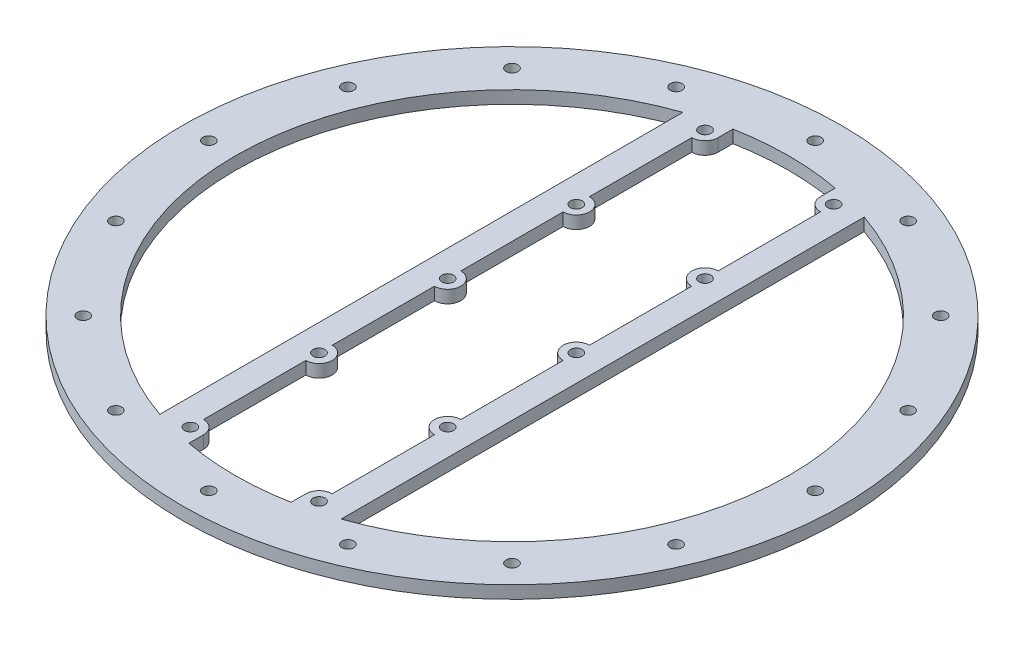
SolidWorks part; units mm, degrees
ref_plane "Front" through (0, 0, 0) normal (0, 0, 1) x (1, 0, 0)
ref_plane "Top" through (0, 0, 0) normal (0, 1, 0) x (1, 0, 0)
ref_plane "Right" through (0, 0, 0) normal (1, 0, 0) x (0, 0, -1)
sketch "Sketch1" plane through (0, 0, 0) normal (0, 1, 0) x (1, 0, 0)
  line L0 (0, 73.025) -> (0, -73.025) construction
  line L1 (73.025, 0) -> (-73.025, 0) construction
  line L3 (15.494, 64.8498) -> (15.494, -64.8498) construction
  line L4 (-15.494, 64.8498) -> (-15.494, -64.8498) construction
  line L5 (64.8498, -15.494) -> (-64.8498, -15.494) construction
  line L7 (73.025, -15.494) -> (-73.025, -15.494) construction
  line L8 (64.8498, 15.494) -> (-64.8498, 15.494) construction
  circle A0 centre (0, 0) radius 79.375
  circle A1 centre (0, 0) radius 66.675
  circle A2 centre (0, 0) radius 73.025 construction
  circle A3 centre (0, 73.025) radius 1.4224
  circle A4 centre (27.9455, 67.4663) radius 1.4224
  circle A5 centre (51.6365, 51.6365) radius 1.4224
  circle A6 centre (67.4663, 27.9455) radius 1.4224
  circle A7 centre (73.025, 0) radius 1.4224
  circle A8 centre (67.4663, -27.9455) radius 1.4224
  circle A9 centre (51.6365, -51.6365) radius 1.4224
  circle A10 centre (27.9455, -67.4663) radius 1.4224
  circle A11 centre (0, -73.025) radius 1.4224
  circle A12 centre (-27.9455, -67.4663) radius 1.4224
  circle A13 centre (-51.6365, -51.6365) radius 1.4224
  circle A14 centre (-67.4663, -27.9455) radius 1.4224
  circle A15 centre (-73.025, 0) radius 1.4224
  circle A16 centre (-67.4663, 27.9455) radius 1.4224
  circle A17 centre (-51.6365, 51.6365) radius 1.4224
  circle A18 centre (-27.9455, 67.4663) radius 1.4224
  point P40 (0, 0)
  dimension "D1" = 158.75
  dimension "D2" = 133.35
  dimension "D3" = 146.05
  dimension "D4" = 2.8448
  dimension "D6" = 15.494
  dimension "D8" = 15.494
  dimension "D9" = 15.494
  dimension "D7" = 15.494
  dimension "D5" = 16
extrude "Boss-Extrude1" add sketch "Sketch1" along normal blind 3.048
sketch "Sketch2" plane through (0, 3.048, 0) normal (0, 1, 0) x (1, 0, 0)
  line L0 (0, 66.675) -> (0, -66.675) construction
  line L1 (-15.494, 27.813) -> (-15.494, 3.175)
  line L2 (-15.494, 58.801) -> (-15.494, 34.163)
  line L3 (-15.494, 64.8498) -> (-15.494, -64.8498) construction
  line L4 (-21.844, 62.9952) -> (-21.844, -62.9952)
  line L5 (21.844, -62.9952) -> (21.844, 62.9952)
  line L6 (-15.494, -3.175) -> (-15.494, -27.813)
  line L7 (-15.494, -34.163) -> (-15.494, -58.801)
  line L8 (15.494, -34.163) -> (15.494, -58.801)
  line L9 (15.494, -3.175) -> (15.494, -27.813)
  line L10 (15.494, 27.813) -> (15.494, 3.175)
  line L11 (15.494, 58.801) -> (15.494, 34.163)
  line L12 (-12.319, 61.976) -> (-12.319, 65.5271)
  line L13 (12.319, 61.976) -> (12.319, 65.5271)
  line L14 (-12.319, -61.976) -> (-12.319, -65.5271)
  line L15 (12.319, -61.976) -> (12.319, -65.5271)
  circle A0 centre (0, 0) radius 66.675 construction
  circle A1 centre (-15.494, 61.976) radius 1.4224
  circle A2 centre (15.494, 61.976) radius 1.4224
  circle A3 centre (-15.494, 30.988) radius 1.4224
  circle A4 centre (15.494, 30.988) radius 1.4224
  circle A5 centre (-15.494, 0) radius 1.4224
  circle A6 centre (15.494, 0) radius 1.4224
  circle A7 centre (-15.494, -30.988) radius 1.4224
  circle A8 centre (15.494, -30.988) radius 1.4224
  circle A9 centre (-15.494, -61.976) radius 1.4224
  circle A10 centre (15.494, -61.976) radius 1.4224
  circle A11 centre (0, 0) radius 66.675 construction
  circle A12 centre (-15.494, 61.976) radius 3.175
  circle A13 centre (-15.494, 30.988) radius 3.175
  circle A14 centre (-15.494, 0) radius 3.175
  circle A15 centre (-15.494, -30.988) radius 3.175
  circle A16 centre (-15.494, -61.976) radius 3.175
  circle A17 centre (15.494, -61.976) radius 3.175
  circle A18 centre (15.494, -30.988) radius 3.175
  circle A19 centre (15.494, 0) radius 3.175
  circle A20 centre (15.494, 30.988) radius 3.175
  circle A21 centre (15.494, 61.976) radius 3.175
  circle M20 centre (0, 0) radius 66.675
  dimension "D3" = 2.8448
  dimension "D6" = 6.35
  dimension "D4" = 5
  dimension "D5" = 30.988
  dimension "D7" = 6.35
  dimension "D1" = 6.35
  dimension "D2" = 15.494
extrude "Boss-Extrude2" add sketch "Sketch2" against normal blind 3.048 contours A16 L14 M20 | A16 A9 M20 | A16 L7 A15 L6 A14 L1 A13 L2 A12 L4 M20 | A17 L15 M20 | A17 A10 M20 | A21 L11 A20 L10 A19 L9 A18 L8 A17 L5 M20 | A18 A8 | A15 A7 | A19 A6 | A14 A5 | A13 A3 | A20 A4 | A21 L13 M20 | A21 A2 M20 | A12 A1 M20 | A12 L12 M20
